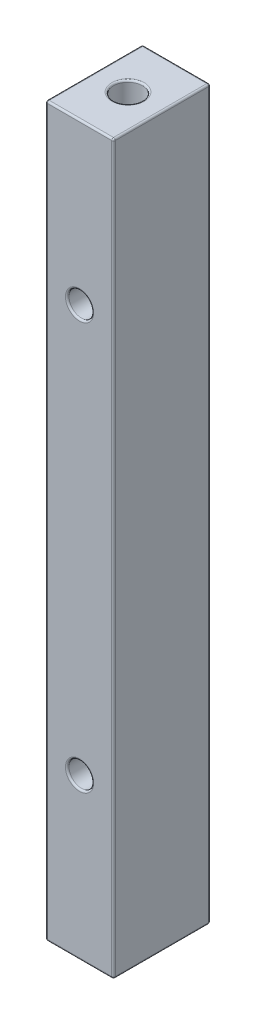
SolidWorks part; units mm, degrees
ref_plane "Front Plane" through (0, 0, 0) normal (0, 0, 1) x (1, 0, 0)
ref_plane "Top Plane" through (0, 0, 0) normal (0, 1, 0) x (1, 0, 0)
ref_plane "Right Plane" through (0, 0, 0) normal (1, 0, 0) x (0, 0, -1)
sketch "Sketch1" plane through (0, 0, 0) normal (0, 1, 0) x (1, 0, 0)
  line L0 (0, 6.7996) -> (0, -6.7996) construction
  line L1 (4.7625, -6.7996) -> (-4.7625, -6.7996)
  line L2 (4.7625, -6.7996) -> (4.7625, 6.7996)
  line L3 (4.7625, 6.7996) -> (-4.7625, 6.7996)
  line L4 (-4.7625, -6.7996) -> (-4.7625, 6.7996)
  circle A0 centre (0, 0) radius 4.7625 construction
  circle A1 centre (0, 0) radius 2.0193
  dimension "D1" = 9.525
  dimension "D2" = 4.0386
  dimension "D3" = 13.5992
  dimension "D4" = 9.525
extrude "Boss-Extrude1" add sketch "Sketch1" along normal mid plane 102.108
sketch "Sketch2" plane through (0, 0, 0) normal (0, 1, 0) x (1, 0, 0)
  circle A0 centre (0, 0) radius 2.0193
  circle A1 centre (0, 0) radius 2.0193 construction
extrude "Boss-Extrude2" add sketch "Sketch2" along normal offset from surface 12.7 and the other way offset from surface (38.354 mm away) 12.7 up to face at (0, 51.054, 0) other way up to face at (0, -51.054, 0)
sketch "Sketch4" plane through (0, 0, -6.7996) normal (0, 0, -1) x (-1, 0, 0)
  line L0 (4.7625, 0) -> (-4.7625, 0) construction
  line L1 (0, 28.575) -> (0, -28.575) construction
  line L2 (4.7625, 51.054) -> (4.7625, -51.054) construction
  line L3 (-4.7625, 51.054) -> (-4.7625, -51.054) construction
  circle A0 centre (0, 28.575) radius 1.7272
  circle A1 centre (0, -28.575) radius 1.7272
  point P8 (0, 0)
  dimension "D2" = 3.4544
  dimension "D1" = 57.15
extrude "Cut-Extrude1" cut sketch "Sketch4" against normal up to surface (13.5992 mm away) up to face at (0, 0, 6.7996)
fillet "Fillet2" radius 0.254 18 edges at (-4.7625, 51.054, 0) (-4.7625, -51.054, 0) (4.7625, 51.054, 0) (4.7625, -51.054, 0) (-4.7625, 0, 6.7996) (0, 51.054, 6.7996) (4.7625, 0, 6.7996) (0, -51.054, 6.7996) (4.7625, 0, -6.7996) (0, 51.054, -6.7996) (-4.7625, 0, -6.7996) (0, -51.054, -6.7996) (0, -51.054, 2.0193) (0, 51.054, 2.0193) (-1.7272, -28.575, 6.7996) (-1.7272, 28.575, 6.7996) (-1.7272, -28.575, -6.7996) (-1.7272, 28.575, -6.7996)
